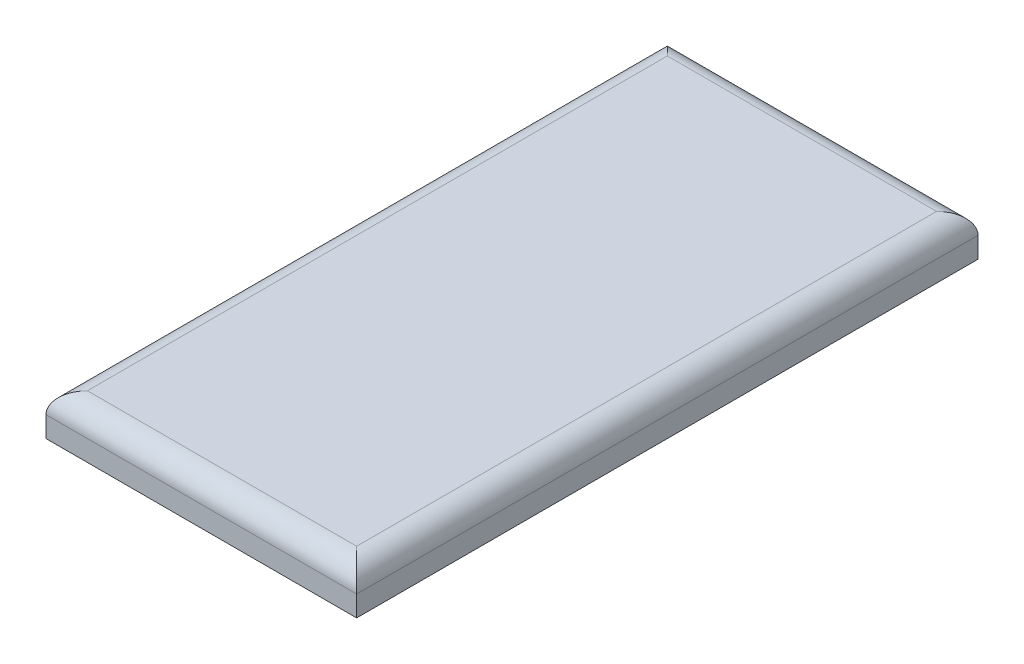
SolidWorks part; units mm, degrees
material "Polyurethane Foam Flexible"
ref_plane "Front Plane" through (0, 0, 0) normal (0, 0, 1) x (1, 0, 0)
ref_plane "Top Plane" through (0, 0, 0) normal (0, 1, 0) x (1, 0, 0)
ref_plane "Right Plane" through (0, 0, 0) normal (1, 0, 0) x (0, 0, -1)
sketch "Sketch1" plane through (0, 0, 0) normal (0, 1, 0) x (1, 0, 0)
  line L1 (-75, -150) -> (75, -150)
  line L2 (-75, -150) -> (-75, 150)
  line L3 (-75, 150) -> (75, 150)
  line L4 (75, -150) -> (75, 150)
  line L5 (-75, -150) -> (75, 150) construction
  line L6 (-75, 150) -> (75, -150) construction
  point P0 (0, 0)
  dimension "D1" = 150
  dimension "D2" = 300
extrude "Boss-Extrude1" add sketch "Sketch1" along normal blind 20
fillet "Fillet1" radius 10 4 edges at (0, 20, 150) (-75, 20, 0) (0, 20, -150) (75, 20, 0)
